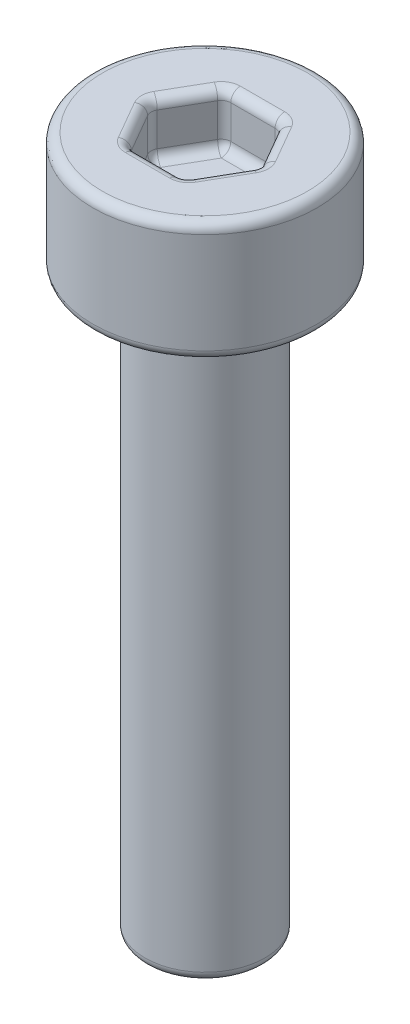
SolidWorks part; units mm, degrees
material "铸造碳钢"
ref_plane "Front" through (0, 0, 0) normal (0, 0, 1) x (1, 0, 0)
ref_plane "Top" through (0, 0, 0) normal (0, 1, 0) x (1, 0, 0)
ref_plane "Right" through (0, 0, 0) normal (1, 0, 0) x (0, 0, -1)
sketch "草图1" plane through (0, 0, 0) normal (0, 1, 0) x (1, 0, 0)
  circle A0 centre (0, 0) radius 1.25
  dimension "螺丝直径" = 2.5
extrude "凸台-拉伸1" add sketch "草图1" against normal blind 12
sketch "草图2" plane through (0, 0, 0) normal (0, 1, 0) x (1, 0, 0)
  circle A0 centre (0, 0) radius 2.34
  dimension "头部直径" = 4.68
extrude "凸台-拉伸2" add sketch "草图2" along normal blind 2.5
sketch "草图3" plane through (0, 2.5, 0) normal (0, 1, 0) x (1, 0, 0)
  line L1 (1.1547, 0) -> (0.5774, 1)
  line L2 (0.5774, 1) -> (-0.5774, 1)
  line L3 (-0.5774, 1) -> (-1.1547, 0)
  line L4 (-1.1547, 0) -> (-0.5774, -1)
  line L5 (-0.5774, -1) -> (0.5774, -1)
  line L6 (0.5774, -1) -> (1.1547, 0)
  circle A0 centre (0, 0) radius 1 construction
  dimension "内六角对边" = 2
extrude "切除-拉伸1" cut sketch "草图3" against normal blind 1.1
fillet "圆角1" radius 0.2 21 edges at (0, 1.4, 1) (0, 2.5, 1) (0.5774, 1.95, 1) (0.866, 1.4, 0.5) (0.866, 2.5, 0.5) (1.1547, 1.95, 0) (0.866, 1.4, -0.5) (0.866, 2.5, -0.5) (-0.866, 1.4, 0.5) (-0.5774, 1.95, 1) (-0.866, 2.5, 0.5) (-0.866, 1.4, -0.5) (-1.1547, 1.95, 0) (-0.866, 2.5, -0.5) (0.5774, 1.95, -1) (0, 1.4, -1) (-0.5774, 1.95, -1) (0, 2.5, -1) (0, 0, 2.34) (0, 2.5, 2.34) (0, -12, 1.25)
